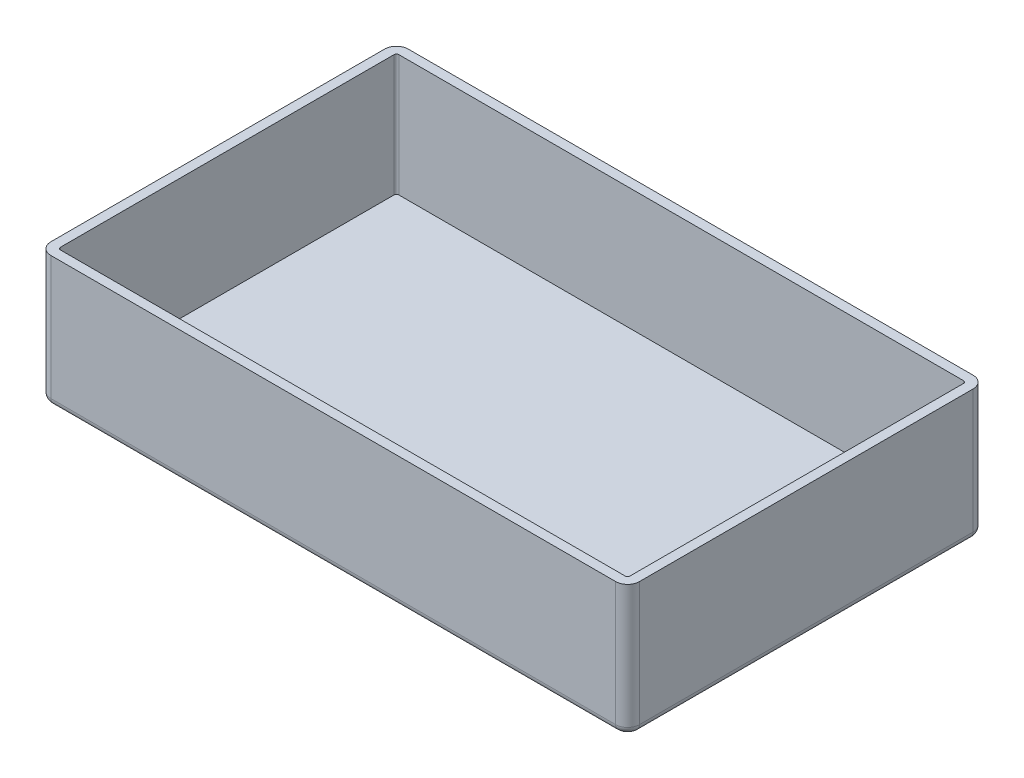
SolidWorks part; units mm, degrees
ref_plane "Plano frontal" through (0, 0, 0) normal (0, 0, 1) x (1, 0, 0)
ref_plane "Plano superior" through (0, 0, 0) normal (0, 1, 0) x (1, 0, 0)
ref_plane "Plano direito" through (0, 0, 0) normal (1, 0, 0) x (0, 0, -1)
sketch "Esboço1" plane through (0, 0, 0) normal (0, 1, 0) x (1, 0, 0)
  line L1 (-123.5, -75) -> (123.5, -75)
  line L2 (-123.5, -75) -> (-123.5, 75)
  line L3 (-123.5, 75) -> (123.5, 75)
  line L4 (123.5, -75) -> (123.5, 75)
  line L5 (-123.5, -75) -> (123.5, 75) construction
  line L6 (-123.5, 75) -> (123.5, -75) construction
  point P0 (0, 0)
  dimension "D1" = 150
  dimension "D2" = 247
extrude "Ressalto-extrusão1" add sketch "Esboço1" along normal blind 55
fillet "Filete1" radius 5 4 edges at (-123.5, 27.5, -75) (-123.5, 27.5, 75) (123.5, 27.5, -75) (123.5, 27.5, 75)
fillet "Filete2" radius 3 8 edges at (122.0355, 0, -73.5355) (123.5, 0, 0) (122.0355, 0, 73.5355) (0, 0, 75) (-122.0355, 0, 73.5355) (-123.5, 0, 0) (-122.0355, 0, -73.5355) (0, 0, -75)
shell "Casca1" thickness 4
